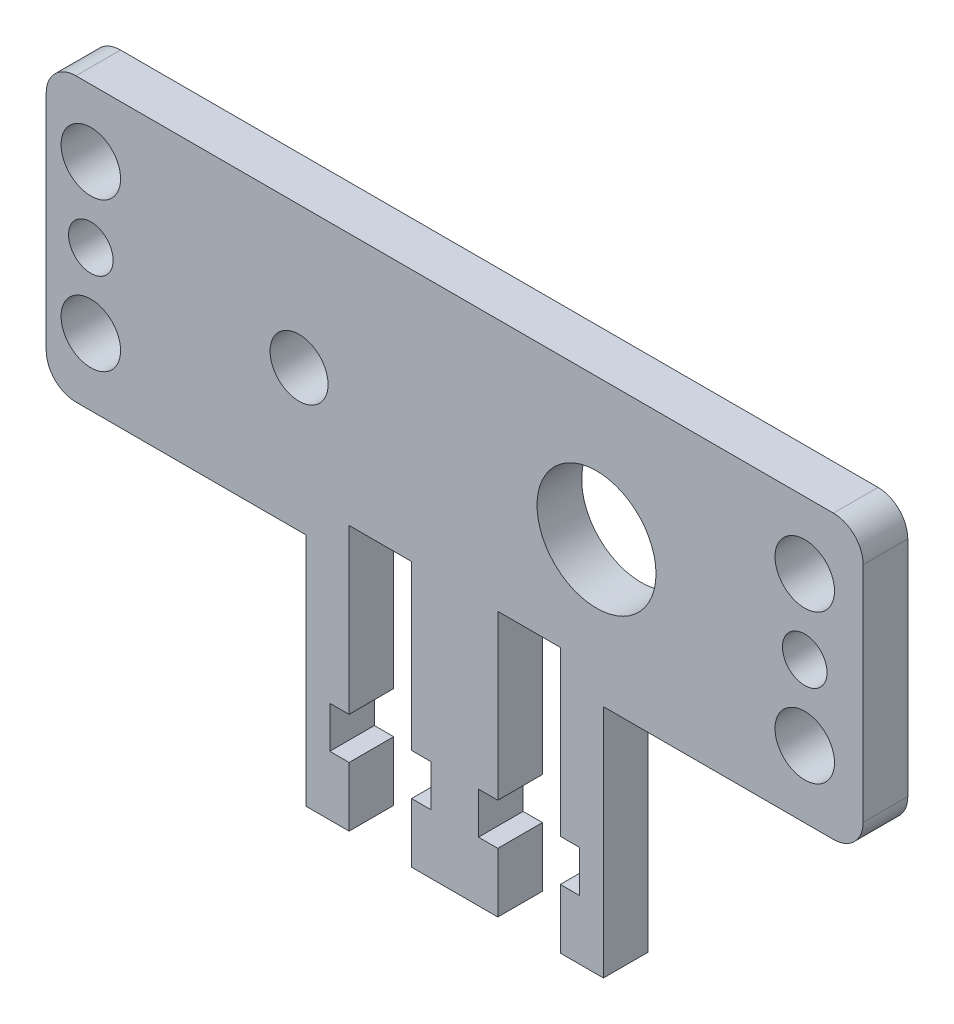
SolidWorks part; units mm, degrees
ref_plane "Front Plane" through (0, 0, 0) normal (0, 0, 1) x (1, 0, 0)
ref_plane "Top Plane" through (0, 0, 0) normal (0, 1, 0) x (1, 0, 0)
ref_plane "Right Plane" through (0, 0, 0) normal (1, 0, 0) x (0, 0, -1)
sketch "Sketch1" plane through (0, 0, -5.5516) normal (0, 0, 1) x (1, 0, 0)
  line L0 (-25.4646, 10.1373) -> (25.4646, 10.1373)
  line L1 (-27.4646, 8.1373) -> (-27.4646, -6.8627)
  line L2 (27.4646, 8.1373) -> (27.4646, -6.8627)
  line L3 (-25.4646, -8.8627) -> (-10, -8.8627)
  line L4 (-20.7646, 10.1373) -> (-25.9646, 10.1373) construction
  line L5 (-20.7646, -8.8627) -> (-25.9646, -8.8627) construction
  line L6 (-27.4646, -2.971) -> (-27.4646, 4.2457) construction
  line L8 (-27.4646, 0.6373) -> (27.4646, 0.6373) construction
  line L9 (-24.4646, 10.1373) -> (-24.4646, -8.8627) construction
  line L10 (23.5354, 10.1373) -> (23.5354, -8.8627) construction
  line L27 (-7.1, -24.6627) -> (-2.9, -24.6627) construction
  line L28 (-7.1, -24.6627) -> (-7.1, -20.6627)
  line L40 (-5, -24.6627) -> (-5, -6.8627) construction
  line L41 (10, -8.8627) -> (25.4646, -8.8627)
  line L42 (-7.1, -6.8627) -> (-2.9, -6.8627)
  line L44 (-7.1, -17.8627) -> (-8.4, -17.8627)
  line L46 (-8.4, -17.8627) -> (-8.4, -20.6627)
  line L47 (-7.1, -20.6627) -> (-8.4, -20.6627)
  line L48 (-7.1, -17.8627) -> (-7.1, -6.8627)
  line L49 (-2.9, -17.8627) -> (-2.9, -6.8627)
  line L50 (-2.9, -20.6627) -> (-1.6, -20.6627)
  line L51 (-1.6, -17.8627) -> (-1.6, -20.6627)
  line L52 (-2.9, -17.8627) -> (-1.6, -17.8627)
  line L53 (-2.9, -24.6627) -> (-2.9, -20.6627)
  line L54 (2.9, -24.6627) -> (7.1, -24.6627) construction
  line L55 (2.9, -24.6627) -> (2.9, -20.6627)
  line L56 (5, -24.6627) -> (5, -6.8627) construction
  line L57 (2.9, -6.8627) -> (7.1, -6.8627)
  line L58 (2.9, -17.8627) -> (1.6, -17.8627)
  line L59 (1.6, -17.8627) -> (1.6, -20.6627)
  line L60 (2.9, -20.6627) -> (1.6, -20.6627)
  line L61 (2.9, -17.8627) -> (2.9, -6.8627)
  line L62 (7.1, -17.8627) -> (7.1, -6.8627)
  line L63 (7.1, -20.6627) -> (8.4, -20.6627)
  line L64 (8.4, -17.8627) -> (8.4, -20.6627)
  line L65 (7.1, -17.8627) -> (8.4, -17.8627)
  line L66 (7.1, -24.6627) -> (7.1, -20.6627)
  line L67 (-10, -8.8627) -> (-10, -24.6627)
  line L69 (10, -24.6627) -> (10, -8.8627)
  line L70 (0, 10.1373) -> (0, -24.6627) construction
  line L71 (-10, -24.6627) -> (-7.1, -24.6627)
  line L72 (-2.9, -24.6627) -> (0, -24.6627)
  line L73 (0, -24.6627) -> (2.9, -24.6627)
  line L74 (7.1, -24.6627) -> (10, -24.6627)
  arc A0 (25.4646, 10.1373) -> (27.4646, 8.1373) centre (25.4646, 8.1373) cw
  arc A1 (27.4646, -6.8627) -> (25.4646, -8.8627) centre (25.4646, -6.8627) cw
  arc A2 (-27.4646, -6.8627) -> (-25.4646, -8.8627) centre (-25.4646, -6.8627) ccw
  arc A3 (-27.4646, 8.1373) -> (-25.4646, 10.1373) centre (-25.4646, 8.1373) cw
  circle A4 centre (-24.4646, 5.6373) radius 2
  circle A5 centre (-24.4646, -4.3627) radius 2
  circle A6 centre (23.5354, -4.3627) radius 2
  circle A7 centre (23.5354, 5.6373) radius 2
  arc A8 (-26.1261, 4.524) -> (-25.9958, 6.924) centre (-24.4646, 5.6373) ccw construction
  arc A10 (-25.9958, -5.6494) -> (-26.1261, -3.2494) centre (-24.4646, -4.3627) ccw construction
  arc A11 (25.0665, 6.924) -> (25.1969, 4.524) centre (23.5354, 5.6373) ccw construction
  circle A12 centre (9.5354, 0.6373) radius 4
  circle A13 centre (-10.4646, 0.6373) radius 1.95
  circle A14 centre (-24.4646, 0.6373) radius 1.5
  circle A15 centre (23.5354, 0.6373) radius 1.5
  arc A16 (25.1969, -3.2494) -> (25.0665, -5.6494) centre (23.5354, -4.3627) ccw construction
  circle A17 centre (9.5354, 0.6373) radius 5 construction
  dimension "D1" = 2
  dimension "D2" = 8
  dimension "D3" = 3.9
  dimension "D4" = 3
  dimension "D5" = 3
  dimension "D6" = 4.2
  dimension "D7" = 4
  dimension "D8" = 11
  dimension "D9" = 2.8
  dimension "D10" = 1.3
  dimension "D11" = 4.2
  dimension "D12" = 4
  dimension "D13" = 11
  dimension "D14" = 2.8
  dimension "D15" = 1.3
  dimension "D16" = 10
  dimension "D17" = 20
  dimension "D18" = 5
  dimension "D19" = 7.5
  dimension "D20" = 20
extrude "Boss-Extrude1" add sketch "Sketch1" along normal blind 3
